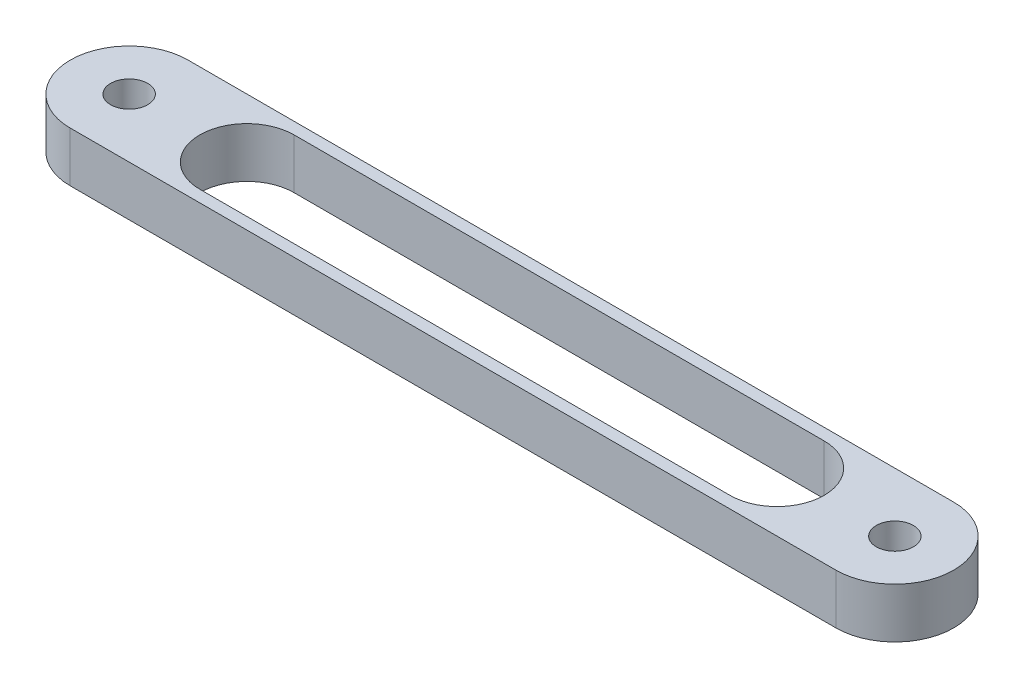
SolidWorks part; units mm, degrees
ref_plane "Plan de face" through (0, 0, 0) normal (0, 0, 1) x (1, 0, 0)
ref_plane "Plan de dessus" through (0, 0, 0) normal (0, 1, 0) x (1, 0, 0)
ref_plane "Plan de droite" through (0, 0, 0) normal (1, 0, 0) x (0, 0, -1)
sketch "Esquisse1" plane through (0, 0, 0) normal (0, 1, 0) x (1, 0, 0)
  line L0 (0, 10) -> (130, 10)
  line L1 (0, -10) -> (130, -10)
  line L2 (20, 8) -> (110, 8)
  line L3 (20, -8) -> (110, -8)
  line L4 (0, 0) -> (20, 0) construction
  arc A0 (0, 10) -> (0, -10) centre (0, 0) ccw
  arc A1 (130, -10) -> (130, 10) centre (130, 0) ccw
  arc A2 (20, 8) -> (20, -8) centre (20, 0) ccw
  arc A3 (110, -8) -> (110, 8) centre (110, 0) ccw
  dimension "D1" = 10
  dimension "D4" = 8
  dimension "D7" = 8
  dimension "D3" = 10
  dimension "D2" = 130
  dimension "D5" = 20
  dimension "D6" = 20
extrude "Boss.-Extru.1" add sketch "Esquisse1" along normal mid plane 8.5
sketch "Esquisse2" plane through (0, 4.25, 0) normal (0, 1, 0) x (1, 0, 0)
  line L0 (65, 10) -> (65, -10) construction
  line L1 (130, 10) -> (0, 10) construction
  line L2 (0, -10) -> (130, -10) construction
  circle A0 centre (0, 0) radius 3.15
  circle A1 centre (130, 0) radius 3.15
  dimension "D1" = 6.3
extrude "Enlèv. mat.-Extru.1" cut sketch "Esquisse2" against normal through all
